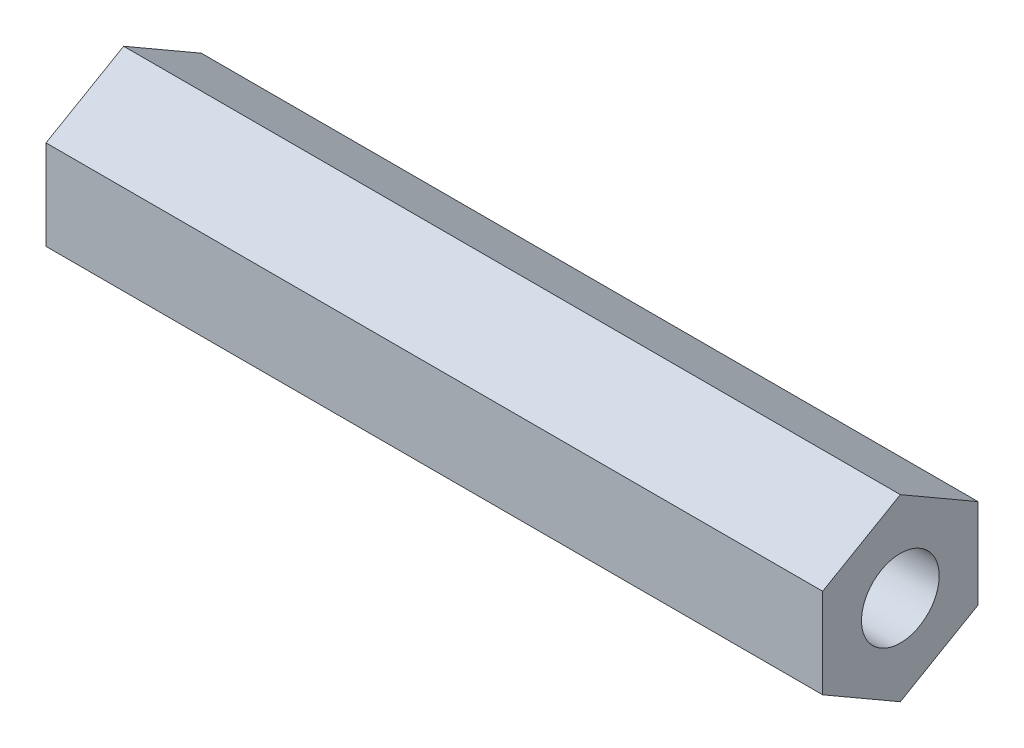
SolidWorks part; units mm, degrees
ref_plane "Front Plane" through (0, 0, 0) normal (0, 0, 1) x (1, 0, 0)
ref_plane "Top Plane" through (0, 0, 0) normal (0, 1, 0) x (1, 0, 0)
ref_plane "Right Plane" through (0, 0, 0) normal (1, 0, 0) x (0, 0, -1)
sketch "Sketch1" plane through (0, 0, 0) normal (1, 0, 0) x (0, 0, -1)
  line L7 (-42.7283, 8.2771) -> (-45.7283, 6.5451)
  line L8 (-45.7283, 6.5451) -> (-45.7283, 3.081)
  line L9 (-45.7283, 3.081) -> (-42.7283, 1.3489)
  line L10 (-42.7283, 1.3489) -> (-39.7283, 3.081)
  line L11 (-39.7283, 3.081) -> (-39.7283, 6.5451)
  line L12 (-39.7283, 6.5451) -> (-42.7283, 8.2771)
  circle A0 centre (-42.7283, 4.813) radius 1.5
  circle A2 centre (-42.7283, 4.813) radius 3 construction
  dimension "D1" = 3
extrude "Boss-Extrude1" add sketch "Sketch1" along normal blind 30
